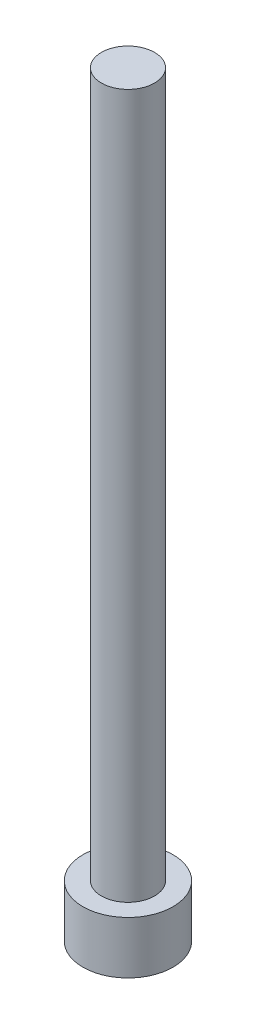
SolidWorks part; units mm, degrees
ref_plane "Front Plane" through (0, 0, 0) normal (0, 0, 1) x (1, 0, 0)
ref_plane "Top Plane" through (0, 0, 0) normal (0, 1, 0) x (1, 0, 0)
ref_plane "Right Plane" through (0, 0, 0) normal (1, 0, 0) x (0, 0, -1)
sketch "Sketch1" plane through (0, 0, 0) normal (0, 1, 0) x (1, 0, 0)
  circle A0 centre (0, 0) radius 6.4
  dimension "D1" = 12.8
extrude "Boss-Extrude1" add sketch "Sketch1" along normal blind 7.45
sketch "Sketch2" plane through (0, 7.45, 0) normal (0, 1, 0) x (1, 0, 0)
  circle A0 centre (0, 0) radius 3.775
  dimension "D1" = 7.55
extrude "Boss-Extrude2" add sketch "Sketch2" along normal blind 100
sketch "Sketch3" plane through (0, 0, 0) normal (0, -1, 0) x (1, 0, 0)
  line L1 (-3.6084, 0) -> (-1.8042, -3.125)
  line L2 (-1.8042, -3.125) -> (1.8042, -3.125)
  line L3 (1.8042, -3.125) -> (3.6084, 0)
  line L4 (3.6084, 0) -> (1.8042, 3.125)
  line L5 (1.8042, 3.125) -> (-1.8042, 3.125)
  line L6 (-1.8042, 3.125) -> (-3.6084, 0)
  circle A0 centre (0, 0) radius 3.125 construction
  dimension "D1" = 6.25
extrude "Cut-Extrude1" cut sketch "Sketch3" against normal blind 5
fillet "Fillet2" radius 0.5 6 edges at (0, 0, -3.125) (-2.7063, 0, -1.5625) (-2.7063, 0, 1.5625) (0, 0, 3.125) (2.7063, 0, 1.5625) (2.7063, 0, -1.5625)
fillet "Fillet3" radius 0.5 6 edges at (0, 5, -3.125) (2.7063, 5, -1.5625) (2.7063, 5, 1.5625) (0, 5, 3.125) (-2.7063, 5, -1.5625) (-2.7063, 5, 1.5625)
